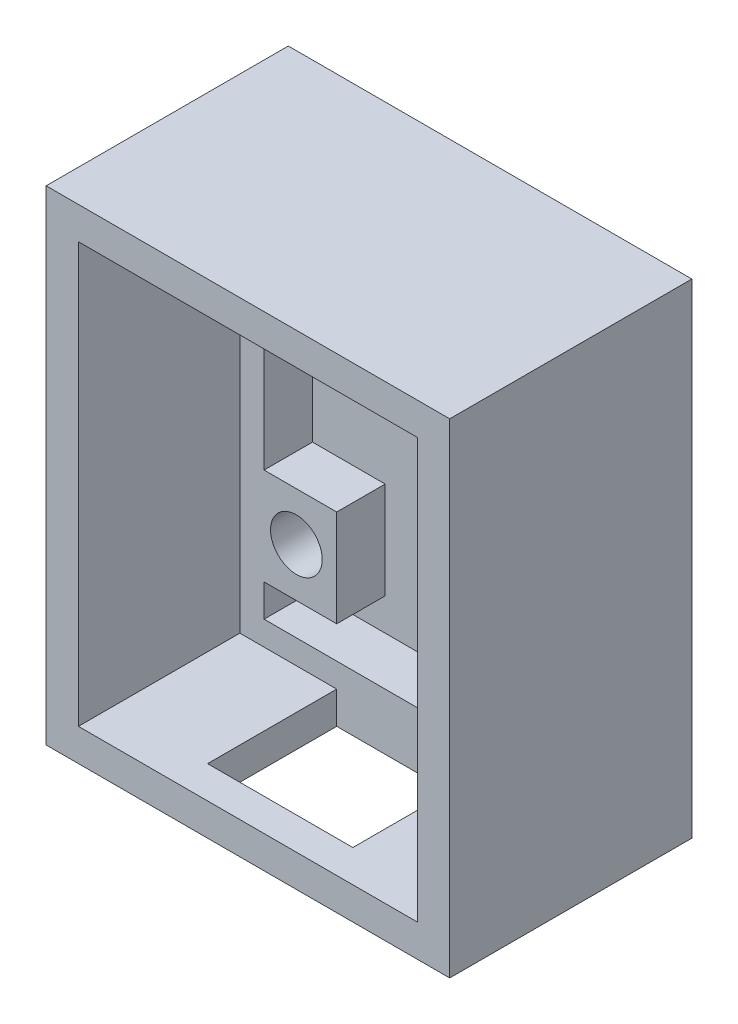
SolidWorks part; units mm, degrees
ref_plane "正面" through (0, 0, 0) normal (0, 0, 1) x (1, 0, 0)
ref_plane "平面" through (0, 0, 0) normal (0, 1, 0) x (1, 0, 0)
ref_plane "右側面" through (0, 0, 0) normal (1, 0, 0) x (0, 0, -1)
sketch "ｽｹｯﾁ1" plane through (0, 0, 0) normal (0, 0, 1) x (1, 0, 0)
  line L1 (-83.9031, 40.6786) -> (-58.9031, 40.6786)
  line L2 (-83.9031, 40.6786) -> (-83.9031, 10.6786)
  line L3 (-83.9031, 10.6786) -> (-58.9031, 10.6786)
  line L4 (-58.9031, 40.6786) -> (-58.9031, 10.6786)
  dimension "D1" = 30
  dimension "D2" = 25
extrude "ﾎﾞｽ - 押し出し1" add sketch "ｽｹｯﾁ1" along normal blind 15
sketch "ｽｹｯﾁ2" plane through (0, 0, 15) normal (0, 0, 1) x (1, 0, 0)
  line L0 (-58.9031, 40.6786) -> (-83.9031, 40.6786) construction
  line L1 (-81.9031, 38.6786) -> (-60.9031, 38.6786)
  line L2 (-81.9031, 38.6786) -> (-81.9031, 12.6786)
  line L3 (-81.9031, 12.6786) -> (-60.9031, 12.6786)
  line L4 (-60.9031, 38.6786) -> (-60.9031, 12.6786)
  line L5 (-83.9031, 10.6786) -> (-58.9031, 10.6786) construction
  line L6 (-58.9031, 10.6786) -> (-58.9031, 40.6786) construction
  line L7 (-83.9031, 40.6786) -> (-83.9031, 10.6786) construction
  dimension "D1" = 26
  dimension "D2" = 21
  dimension "D3" = 2
  dimension "D4" = 2
  dimension "D5" = 2
  dimension "D6" = 2
extrude "ｶｯﾄ - 押し出し1" cut sketch "ｽｹｯﾁ2" against normal blind 13
sketch "ｽｹｯﾁ3" plane through (0, 0, 2) normal (0, 0, 1) x (1, 0, 0)
  line L1 (-60.9031, 38.6786) -> (-81.9031, 38.6786)
  line L2 (-60.9031, 38.6786) -> (-60.9031, 12.6786)
  line L3 (-60.9031, 12.6786) -> (-81.9031, 12.6786)
  line L4 (-81.9031, 38.6786) -> (-81.9031, 12.6786)
  line L5 (-80.4031, 37.1786) -> (-62.4031, 37.1786)
  line L6 (-80.4031, 37.1786) -> (-80.4031, 14.1786)
  line L7 (-80.4031, 14.1786) -> (-62.4031, 14.1786)
  line L8 (-62.4031, 37.1786) -> (-62.4031, 14.1786)
  dimension "D1" = 1.5
  dimension "D2" = 1.5
  dimension "D3" = 1.5
  dimension "D4" = 1.5
extrude "ﾎﾞｽ - 押し出し2" add sketch "ｽｹｯﾁ3" along normal blind 3
sketch "ｽｹｯﾁ5" plane through (0, 0, 2) normal (0, 0, 1) x (1, 0, 0)
  line L0 (-62.4031, 14.1786) -> (-62.4031, 37.1786) construction
  line L1 (-62.4031, 22.1786) -> (-66.9031, 22.1786)
  line L2 (-62.4031, 22.1786) -> (-62.4031, 16.1786)
  line L3 (-62.4031, 16.1786) -> (-66.9031, 16.1786)
  line L4 (-66.9031, 22.1786) -> (-66.9031, 16.1786)
  line L6 (-81.9031, 12.6786) -> (-60.9031, 12.6786) construction
  line L7 (-80.4031, 37.1786) -> (-80.4031, 14.1786) construction
  line L8 (-80.4031, 22.1786) -> (-75.9031, 22.1786)
  line L9 (-80.4031, 22.1786) -> (-80.4031, 16.1786)
  line L10 (-80.4031, 16.1786) -> (-75.9031, 16.1786)
  line L11 (-75.9031, 22.1786) -> (-75.9031, 16.1786)
  point P10 (-66.9031, 19.1786)
  point P15 (-75.9031, 19.1786)
  dimension "D1" = 4.5
  dimension "D2" = 6
  dimension "D3" = 6.5
  dimension "D4" = 6.5
extrude "ﾎﾞｽ - 押し出し3" add sketch "ｽｹｯﾁ5" along normal blind 3
sketch "ｽｹｯﾁ6" plane through (0, 0, 5) normal (0, 0, 1) x (1, 0, 0)
  line L0 (-66.9031, 22.1786) -> (-66.9031, 16.1786) construction
  line L1 (-66.9031, 16.1786) -> (-62.4031, 16.1786) construction
  line L2 (-75.9031, 16.1786) -> (-75.9031, 22.1786) construction
  line L3 (-80.4031, 16.1786) -> (-75.9031, 16.1786) construction
  circle A0 centre (-64.4031, 19.1786) radius 1.6
  circle A1 centre (-78.4031, 19.1786) radius 1.6
  dimension "D1" = 3.2
  dimension "D4" = 2.5
  dimension "D5" = 3
  dimension "D2" = 2.5
  dimension "D3" = 3
extrude "ｶｯﾄ - 押し出し2" cut sketch "ｽｹｯﾁ6" against normal through all
sketch "ｽｹｯﾁ7" plane through (0, 12.6786, 0) normal (0, 1, 0) x (1, 0, 0)
  line L0 (-81.9031, -5) -> (-60.9031, -5) construction
  line L1 (-66.9031, -5) -> (-75.9031, -5)
  line L2 (-66.9031, -5) -> (-66.9031, -13)
  line L3 (-66.9031, -13) -> (-75.9031, -13)
  line L4 (-75.9031, -5) -> (-75.9031, -13)
  line L5 (-81.9031, -15) -> (-60.9031, -15) construction
  line L6 (-60.9031, -5) -> (-60.9031, -15) construction
  line L7 (-81.9031, -5) -> (-81.9031, -15) construction
  dimension "D1" = 2
  dimension "D2" = 6
  dimension "D3" = 6
extrude "ｶｯﾄ - 押し出し3" cut sketch "ｽｹｯﾁ7" against normal through all
